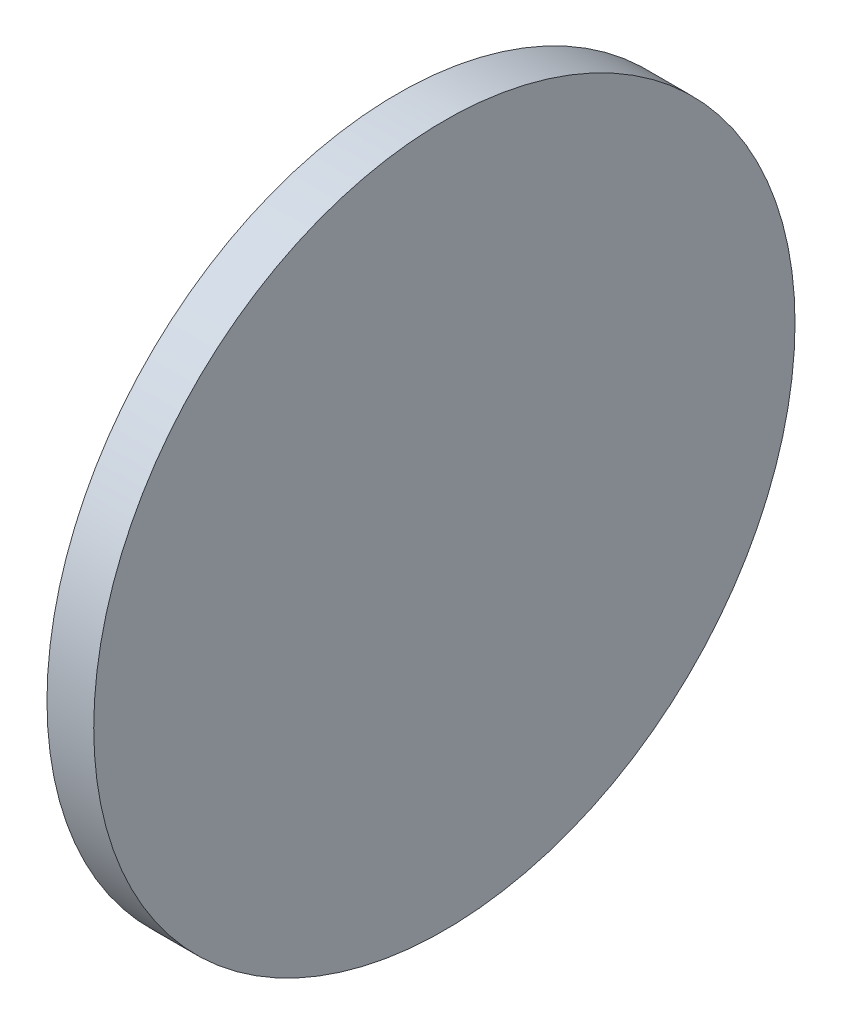
SolidWorks part; units mm, degrees
ref_plane "Front Plane" through (0, 0, 0) normal (0, 0, 1) x (1, 0, 0)
ref_plane "Top Plane" through (0, 0, 0) normal (0, 1, 0) x (1, 0, 0)
ref_plane "Right Plane" through (0, 0, 0) normal (1, 0, 0) x (0, 0, -1)
sketch "Sketch1" plane through (0, 0, 0) normal (1, 0, 0) x (0, 0, -1)
  circle A0 centre (0, 0) radius 7.5
  dimension "D1" = 15
extrude "Boss-Extrude1" add sketch "Sketch1" along normal blind 1
